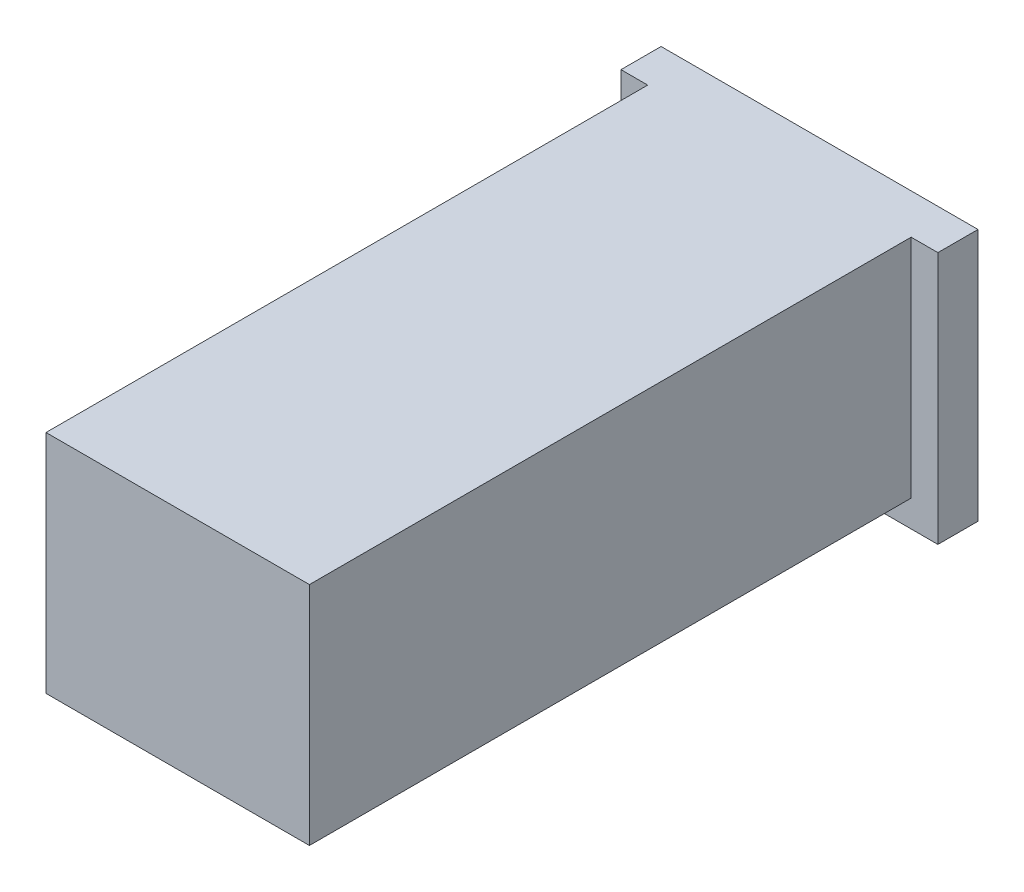
SolidWorks part; units mm, degrees
ref_plane "Alzado" through (0, 0, 0) normal (0, 0, 1) x (1, 0, 0)
ref_plane "Planta" through (0, 0, 0) normal (0, 1, 0) x (1, 0, 0)
ref_plane "Vista lateral" through (0, 0, 0) normal (1, 0, 0) x (0, 0, -1)
sketch "Croquis1" plane through (0, 0, 0) normal (0, 0, 1) x (1, 0, 0)
  line L1 (-492.5, -422.5) -> (492.5, -422.5)
  line L2 (-492.5, -422.5) -> (-492.5, 422.5)
  line L3 (-492.5, 422.5) -> (492.5, 422.5)
  line L4 (492.5, -422.5) -> (492.5, 422.5)
  line L5 (-492.5, -422.5) -> (492.5, 422.5) construction
  line L6 (-492.5, 422.5) -> (492.5, -422.5) construction
  line L7 (-422.5, -352.5) -> (422.5, -352.5)
  line L8 (-422.5, -352.5) -> (-422.5, 352.5)
  line L9 (-422.5, 352.5) -> (422.5, 352.5)
  line L10 (422.5, -352.5) -> (422.5, 352.5)
  line L11 (-422.5, -352.5) -> (422.5, 352.5) construction
  line L12 (-422.5, 352.5) -> (422.5, -352.5) construction
  point P0 (0, 0)
  point P6 (0, 0)
  dimension "D1" = 985
  dimension "D2" = 845
  dimension "D3" = 70
  dimension "D4" = 70
extrude "Saliente-Extruir1" add sketch "Croquis1" along normal blind 95
sketch "Croquis2" plane through (0, 0, 95) normal (0, 0, 1) x (1, 0, 0)
  line L0 (-492.5, -422.5) -> (-442.5, -422.5)
  line L1 (-492.5, -422.5) -> (492.5, -422.5) construction
  line L2 (-442.5, -422.5) -> (-442.5, -405.5)
  line L3 (-442.5, -405.5) -> (-416.5, -405.5)
  line L4 (-416.5, -405.5) -> (-416.5, -403.5)
  line L5 (-416.5, -403.5) -> (-444.5, -403.5)
  line L6 (-444.5, -403.5) -> (-444.5, -420.5)
  line L7 (-444.5, -420.5) -> (-490.5, -420.5)
  line L8 (-490.5, -420.5) -> (-490.5, 420.5)
  line L9 (-492.5, 422.5) -> (-492.5, -422.5) construction
  line L10 (-492.5, -422.5) -> (-492.5, 422.5)
  line L11 (492.5, 422.5) -> (-492.5, 422.5) construction
  line L12 (-490.5, 420.5) -> (490.5, 420.5)
  line L13 (492.5, 422.5) -> (-492.5, 422.5)
  line L14 (492.5, 422.5) -> (492.5, -422.5)
  line L15 (490.5, 420.5) -> (490.5, -405.5)
  line L16 (492.5, -422.5) -> (442.5, -422.5)
  line L17 (442.5, -422.5) -> (442.5, -405.5)
  line L18 (442.5, -405.5) -> (416.5, -405.5)
  line L19 (416.5, -405.5) -> (416.5, -403.5)
  line L20 (416.5, -403.5) -> (444.5, -403.5)
  line L21 (444.5, -403.5) -> (444.5, -420.5)
  line L22 (444.5, -420.5) -> (490.5, -420.5)
  line L23 (490.5, -420.5) -> (490.5, -405.5)
  dimension "D1" = 50
  dimension "D2" = 17
  dimension "D3" = 26
  dimension "D4" = 2
  dimension "D5" = 2
  dimension "D6" = 2
  dimension "D7" = 2
  dimension "D8" = 2
  dimension "D9" = 2
  dimension "D10" = 50
  dimension "D11" = 17
  dimension "D12" = 26
  dimension "D13" = 2
  dimension "D14" = 2
  dimension "D15" = 2
extrude "Saliente-Extruir2" add sketch "Croquis2" along normal blind 1905
sketch "Croquis4" plane through (0, 0, 95) normal (0, 0, 1) x (1, 0, 0)
  line L0 (-442.5, -405.5) -> (-442.5, -407.5)
  line L1 (-442.5, -422.5) -> (-442.5, -405.5) construction
  line L2 (-442.5, -407.5) -> (-414.5, -407.5)
  line L3 (-416.5, -405.5) -> (-416.5, -403.5) construction
  line L4 (-414.5, -407.5) -> (-414.5, -357.5)
  line L5 (-442.5, -405.5) -> (-416.5, -405.5)
  line L6 (-416.5, -405.5) -> (-416.5, -357.5)
  line L8 (0, -422.5) -> (0, -296.3309) construction
  line L9 (-442.5, -422.5) -> (442.5, -422.5) construction
  line L11 (416.5, -405.5) -> (416.5, -357.5)
  line L12 (442.5, -405.5) -> (416.5, -405.5)
  line L13 (414.5, -407.5) -> (414.5, -357.5)
  line L14 (442.5, -407.5) -> (414.5, -407.5)
  line L15 (442.5, -405.5) -> (442.5, -407.5)
  line L16 (-414.5, -357.5) -> (414.5, -357.5)
  line L17 (416.5, -357.5) -> (416.5, -355.5)
  line L18 (416.5, -355.5) -> (-416.5, -355.5)
  line L19 (-416.5, -355.5) -> (-416.5, -357.5)
  dimension "D1" = 2
  dimension "D2" = 2
  dimension "D3" = 50
  dimension "D4" = 2
extrude "Saliente-Extruir4" add sketch "Croquis4" along normal blind 1903
sketch "Croquis3" plane through (0, 422.5, 0) normal (0, 1, 0) x (1, 0, 0)
  line L0 (492.5, -2000) -> (-492.5, -2000)
  line L1 (-492.5, -2000) -> (-492.5, -1998)
  line L2 (-492.5, -2000) -> (-492.5, 0) construction
  line L3 (-492.5, -1998) -> (492.5, -1998)
  line L4 (492.5, -2000) -> (492.5, 0) construction
  line L5 (492.5, -1998) -> (492.5, -2000)
  dimension "D1" = 2
extrude "Saliente-Extruir3" add sketch "Croquis3" against normal up to surface (845 mm away) up to face at (0, -422.5, 1023.75)
sketch "Croquis5" plane through (0, -357.5, 0) normal (0, -1, 0) x (1, 0, 0)
  line L0 (-414.5, 1998) -> (-414.5, 95) construction
  line L1 (-166.5, 1523) -> (166.5, 1523)
  line L2 (-166.5, 1523) -> (-166.5, 1905)
  line L3 (-166.5, 1905) -> (166.5, 1905)
  line L4 (166.5, 1523) -> (166.5, 1905)
  line L5 (-166.5, 1523) -> (166.5, 1905) construction
  line L6 (-166.5, 1905) -> (166.5, 1523) construction
  line L9 (-442.5, 1998) -> (442.5, 1998) construction
  point P0 (0, 1714)
  dimension "D1" = 382
  dimension "D2" = 333
  dimension "D3" = 248
  dimension "D4" = 93
extrude "Saliente-Extruir5" add sketch "Croquis5" along normal blind 20
sketch "Croquis6" plane through (0, -377.5, 0) normal (0, -1, 0) x (1, 0, 0)
  line L0 (166.5, 1905) -> (-166.5, 1905) construction
  line L1 (-151.5, 1538) -> (151.5, 1538)
  line L2 (-151.5, 1538) -> (-151.5, 1890)
  line L3 (-151.5, 1890) -> (151.5, 1890)
  line L4 (151.5, 1538) -> (151.5, 1890)
  line L5 (-151.5, 1538) -> (151.5, 1890) construction
  line L6 (-151.5, 1890) -> (151.5, 1538) construction
  line L7 (166.5, 1523) -> (166.5, 1905) construction
  line L8 (-166.5, 1905) -> (-166.5, 1523) construction
  line L9 (-166.5, 1523) -> (166.5, 1523) construction
  point P0 (0, 1714)
  dimension "D1" = 15
  dimension "D2" = 15
  dimension "D3" = 15
  dimension "D4" = 15
extrude "Saliente-Extruir6" add sketch "Croquis6" along normal blind 20
sketch "Croquis9" plane through (0, -397.5, 0) normal (0, -1, 0) x (1, 0, 0)
  line L1 (-34.1154, 1823.4833) -> (-15.8109, 1823.4833)
  line L2 (-34.1154, 1823.4833) -> (-34.1154, 1871.8073)
  line L3 (-34.1154, 1871.8073) -> (-15.8109, 1871.8073)
  line L4 (-15.8109, 1823.4833) -> (-15.8109, 1871.8073)
  line L5 (-34.1154, 1823.4833) -> (-15.8109, 1871.8073) construction
  line L6 (-34.1154, 1871.8073) -> (-15.8109, 1823.4833) construction
  line L7 (-8.7172, 1823.4833) -> (8.7172, 1823.4833)
  line L8 (-8.7172, 1823.4833) -> (-8.7172, 1871.8073)
  line L9 (-8.7172, 1871.8073) -> (8.7172, 1871.8073)
  line L10 (8.7172, 1823.4833) -> (8.7172, 1871.8073)
  line L11 (-8.7172, 1823.4833) -> (8.7172, 1871.8073) construction
  line L12 (-8.7172, 1871.8073) -> (8.7172, 1823.4833) construction
  line L13 (18.2355, 1823.4833) -> (36.54, 1823.4833)
  line L14 (18.2355, 1823.4833) -> (18.2355, 1871.8073)
  line L15 (18.2355, 1871.8073) -> (36.54, 1871.8073)
  line L16 (36.54, 1823.4833) -> (36.54, 1871.8073)
  line L17 (18.2355, 1823.4833) -> (36.54, 1871.8073) construction
  line L18 (18.2355, 1871.8073) -> (36.54, 1823.4833) construction
  line L19 (47.5227, 1823.4833) -> (65.0951, 1823.4833)
  line L20 (47.5227, 1823.4833) -> (47.5227, 1871.8073)
  line L21 (47.5227, 1871.8073) -> (65.0951, 1871.8073)
  line L22 (65.0951, 1823.4833) -> (65.0951, 1871.8073)
  line L23 (47.5227, 1823.4833) -> (65.0951, 1871.8073) construction
  line L24 (47.5227, 1871.8073) -> (65.0951, 1823.4833) construction
  point P0 (-24.9631, 1847.6453)
  point P5 (0, 1847.6453)
  point P10 (27.3878, 1847.6453)
  point P15 (56.3089, 1847.6453)
extrude "Saliente-Extruir8" add sketch "Croquis9" along normal blind 5
sketch "Croquis10" plane through (0, -402.5, 0) normal (0, -1, 0) x (1, 0, 0)
  line L1 (-31.5489, 1864.4494) -> (-29.1067, 1864.4494)
  line L2 (-31.5489, 1864.4494) -> (-31.5489, 1867.7057)
  line L3 (-31.5489, 1867.7057) -> (-29.1067, 1867.7057)
  line L4 (-29.1067, 1864.4494) -> (-29.1067, 1867.7057)
  line L5 (-31.5489, 1864.4494) -> (-29.1067, 1867.7057) construction
  line L6 (-31.5489, 1867.7057) -> (-29.1067, 1864.4494) construction
  line L7 (-26.4609, 1864.4494) -> (-23.6116, 1864.4494)
  line L8 (-26.4609, 1864.4494) -> (-26.4609, 1867.7057)
  line L9 (-26.4609, 1867.7057) -> (-23.6116, 1867.7057)
  line L10 (-23.6116, 1864.4494) -> (-23.6116, 1867.7057)
  line L11 (-26.4609, 1864.4494) -> (-23.6116, 1867.7057) construction
  line L12 (-26.4609, 1867.7057) -> (-23.6116, 1864.4494) construction
  line L13 (-21.2711, 1864.4494) -> (-18.6253, 1864.4494)
  line L14 (-21.2711, 1864.4494) -> (-21.2711, 1867.7057)
  line L15 (-21.2711, 1867.7057) -> (-18.6253, 1867.7057)
  line L16 (-18.6253, 1864.4494) -> (-18.6253, 1867.7057)
  line L17 (-21.2711, 1864.4494) -> (-18.6253, 1867.7057) construction
  line L18 (-21.2711, 1867.7057) -> (-18.6253, 1864.4494) construction
  line L19 (-31.5489, 1857.835) -> (-29.1067, 1857.835)
  line L20 (-31.5489, 1857.835) -> (-31.5489, 1860.6843)
  line L21 (-31.5489, 1860.6843) -> (-29.1067, 1860.6843)
  line L22 (-29.1067, 1857.835) -> (-29.1067, 1860.6843)
  line L23 (-31.5489, 1857.835) -> (-29.1067, 1860.6843) construction
  line L24 (-31.5489, 1860.6843) -> (-29.1067, 1857.835) construction
  line L25 (-26.4609, 1857.835) -> (-23.6116, 1857.835)
  line L26 (-26.4609, 1857.835) -> (-26.4609, 1860.6843)
  line L27 (-26.4609, 1860.6843) -> (-23.6116, 1860.6843)
  line L28 (-23.6116, 1857.835) -> (-23.6116, 1860.6843)
  line L29 (-26.4609, 1857.835) -> (-23.6116, 1860.6843) construction
  line L30 (-26.4609, 1860.6843) -> (-23.6116, 1857.835) construction
  line L31 (-21.2711, 1857.835) -> (-18.6253, 1857.835)
  line L32 (-21.2711, 1857.835) -> (-21.2711, 1860.6843)
  line L33 (-21.2711, 1860.6843) -> (-18.6253, 1860.6843)
  line L34 (-18.6253, 1857.835) -> (-18.6253, 1860.6843)
  line L35 (-21.2711, 1857.835) -> (-18.6253, 1860.6843) construction
  line L36 (-21.2711, 1860.6843) -> (-18.6253, 1857.835) construction
  line L37 (-31.5489, 1852.7469) -> (-29.1067, 1852.7469)
  line L38 (-31.5489, 1852.7469) -> (-31.5489, 1855.1892)
  line L39 (-31.5489, 1855.1892) -> (-29.1067, 1855.1892)
  line L40 (-29.1067, 1852.7469) -> (-29.1067, 1855.1892)
  line L41 (-31.5489, 1852.7469) -> (-29.1067, 1855.1892) construction
  line L42 (-31.5489, 1855.1892) -> (-29.1067, 1852.7469) construction
  line L43 (-26.4609, 1852.7469) -> (-23.6116, 1852.7469)
  line L44 (-26.4609, 1852.7469) -> (-26.4609, 1855.1892)
  line L45 (-26.4609, 1855.1892) -> (-23.6116, 1855.1892)
  line L46 (-23.6116, 1852.7469) -> (-23.6116, 1855.1892)
  line L47 (-26.4609, 1852.7469) -> (-23.6116, 1855.1892) construction
  line L48 (-26.4609, 1855.1892) -> (-23.6116, 1852.7469) construction
  line L49 (-21.2711, 1852.7469) -> (-18.6253, 1852.7469)
  line L50 (-21.2711, 1852.7469) -> (-21.2711, 1855.1892)
  line L51 (-21.2711, 1855.1892) -> (-18.6253, 1855.1892)
  line L52 (-18.6253, 1852.7469) -> (-18.6253, 1855.1892)
  line L53 (-21.2711, 1852.7469) -> (-18.6253, 1855.1892) construction
  line L54 (-21.2711, 1855.1892) -> (-18.6253, 1852.7469) construction
  line L55 (-5.6585, 1864.4494) -> (-2.8545, 1864.4494)
  line L56 (-5.6585, 1864.4494) -> (-5.6585, 1867.7057)
  line L57 (-5.6585, 1867.7057) -> (-2.8545, 1867.7057)
  line L58 (-2.8545, 1864.4494) -> (-2.8545, 1867.7057)
  line L59 (-5.6585, 1864.4494) -> (-2.8545, 1867.7057) construction
  line L60 (-5.6585, 1867.7057) -> (-2.8545, 1864.4494) construction
  line L61 (-0.7515, 1864.4494) -> (2.2527, 1864.4494)
  line L62 (-0.7515, 1864.4494) -> (-0.7515, 1867.7057)
  line L63 (-0.7515, 1867.7057) -> (2.2527, 1867.7057)
  line L64 (2.2527, 1864.4494) -> (2.2527, 1867.7057)
  line L65 (-0.7515, 1864.4494) -> (2.2527, 1867.7057) construction
  line L66 (-0.7515, 1867.7057) -> (2.2527, 1864.4494) construction
  line L67 (4.0553, 1864.4494) -> (6.8593, 1864.4494)
  line L68 (4.0553, 1864.4494) -> (4.0553, 1867.7057)
  line L69 (4.0553, 1867.7057) -> (6.8593, 1867.7057)
  line L70 (6.8593, 1864.4494) -> (6.8593, 1867.7057)
  line L71 (4.0553, 1864.4494) -> (6.8593, 1867.7057) construction
  line L72 (4.0553, 1867.7057) -> (6.8593, 1864.4494) construction
  line L73 (-5.6585, 1857.835) -> (-2.8545, 1857.835)
  line L74 (-5.6585, 1857.835) -> (-5.6585, 1860.6843)
  line L75 (-5.6585, 1860.6843) -> (-2.8545, 1860.6843)
  line L76 (-2.8545, 1857.835) -> (-2.8545, 1860.6843)
  line L77 (-5.6585, 1857.835) -> (-2.8545, 1860.6843) construction
  line L78 (-5.6585, 1860.6843) -> (-2.8545, 1857.835) construction
  line L79 (-0.7515, 1857.835) -> (2.2527, 1857.835)
  line L80 (-0.7515, 1857.835) -> (-0.7515, 1860.6843)
  line L81 (-0.7515, 1860.6843) -> (2.2527, 1860.6843)
  line L82 (2.2527, 1857.835) -> (2.2527, 1860.6843)
  line L83 (-0.7515, 1857.835) -> (2.2527, 1860.6843) construction
  line L84 (-0.7515, 1860.6843) -> (2.2527, 1857.835) construction
  line L85 (4.3181, 1857.835) -> (6.5964, 1857.835)
  line L86 (4.3181, 1857.835) -> (4.3181, 1860.6843)
  line L87 (4.3181, 1860.6843) -> (6.5964, 1860.6843)
  line L88 (6.5964, 1857.835) -> (6.5964, 1860.6843)
  line L89 (4.3181, 1857.835) -> (6.5964, 1860.6843) construction
  line L90 (4.3181, 1860.6843) -> (6.5964, 1857.835) construction
  line L91 (19.493, 1852.7469) -> (22.3312, 1852.7469)
  line L92 (19.493, 1852.7469) -> (19.493, 1855.1892)
  line L93 (19.493, 1855.1892) -> (22.3312, 1855.1892)
  line L94 (22.3312, 1852.7469) -> (22.3312, 1855.1892)
  line L95 (19.493, 1852.7469) -> (22.3312, 1855.1892) construction
  line L96 (19.493, 1855.1892) -> (22.3312, 1852.7469) construction
  line L97 (-5.543, 1852.7469) -> (-2.97, 1852.7469)
  line L98 (-5.543, 1852.7469) -> (-5.543, 1855.1892)
  line L99 (-5.543, 1855.1892) -> (-2.97, 1855.1892)
  line L100 (-2.97, 1852.7469) -> (-2.97, 1855.1892)
  line L101 (-5.543, 1852.7469) -> (-2.97, 1855.1892) construction
  line L102 (-5.543, 1855.1892) -> (-2.97, 1852.7469) construction
  line L103 (-0.7515, 1852.7469) -> (2.2527, 1852.7469)
  line L104 (-0.7515, 1852.7469) -> (-0.7515, 1855.1892)
  line L105 (-0.7515, 1855.1892) -> (2.2527, 1855.1892)
  line L106 (2.2527, 1852.7469) -> (2.2527, 1855.1892)
  line L107 (-0.7515, 1852.7469) -> (2.2527, 1855.1892) construction
  line L108 (-0.7515, 1855.1892) -> (2.2527, 1852.7469) construction
  line L109 (4.3181, 1852.7469) -> (6.5964, 1852.7469)
  line L110 (4.3181, 1852.7469) -> (4.3181, 1855.1892)
  line L111 (4.3181, 1855.1892) -> (6.5964, 1855.1892)
  line L112 (6.5964, 1852.7469) -> (6.5964, 1855.1892)
  line L113 (4.3181, 1852.7469) -> (6.5964, 1855.1892) construction
  line L114 (4.3181, 1855.1892) -> (6.5964, 1852.7469) construction
  line L115 (19.493, 1857.835) -> (22.3312, 1857.835)
  line L116 (19.493, 1857.835) -> (19.493, 1860.6843)
  line L117 (19.493, 1860.6843) -> (22.3312, 1860.6843)
  line L118 (22.3312, 1857.835) -> (22.3312, 1860.6843)
  line L119 (19.493, 1857.835) -> (22.3312, 1860.6843) construction
  line L120 (19.493, 1860.6843) -> (22.3312, 1857.835) construction
  line L121 (19.493, 1864.4494) -> (22.3312, 1864.4494)
  line L122 (19.493, 1864.4494) -> (19.493, 1867.7057)
  line L123 (19.493, 1867.7057) -> (22.3312, 1867.7057)
  line L124 (22.3312, 1864.4494) -> (22.3312, 1867.7057)
  line L125 (19.493, 1864.4494) -> (22.3312, 1867.7057) construction
  line L126 (19.493, 1867.7057) -> (22.3312, 1864.4494) construction
  line L127 (26.32, 1864.6465) -> (29.1933, 1864.6465)
  line L128 (26.32, 1864.6465) -> (26.32, 1867.5086)
  line L129 (26.32, 1867.5086) -> (29.1933, 1867.5086)
  line L130 (29.1933, 1864.6465) -> (29.1933, 1867.5086)
  line L131 (26.32, 1864.6465) -> (29.1933, 1867.5086) construction
  line L132 (26.32, 1867.5086) -> (29.1933, 1864.6465) construction
  line L133 (31.5908, 1864.6465) -> (35.0334, 1864.6465)
  line L134 (31.5908, 1864.6465) -> (31.5908, 1867.5086)
  line L135 (31.5908, 1867.5086) -> (35.0334, 1867.5086)
  line L136 (35.0334, 1864.6465) -> (35.0334, 1867.5086)
  line L137 (31.5908, 1864.6465) -> (35.0334, 1867.5086) construction
  line L138 (31.5908, 1867.5086) -> (35.0334, 1864.6465) construction
  line L139 (26.32, 1857.835) -> (29.1933, 1857.835)
  line L140 (26.32, 1857.835) -> (26.32, 1860.6843)
  line L141 (26.32, 1860.6843) -> (29.1933, 1860.6843)
  line L142 (29.1933, 1857.835) -> (29.1933, 1860.6843)
  line L143 (26.32, 1857.835) -> (29.1933, 1860.6843) construction
  line L144 (26.32, 1860.6843) -> (29.1933, 1857.835) construction
  line L145 (32.1626, 1857.835) -> (34.4616, 1857.835)
  line L146 (32.1626, 1857.835) -> (32.1626, 1860.6843)
  line L147 (32.1626, 1860.6843) -> (34.4616, 1860.6843)
  line L148 (34.4616, 1857.835) -> (34.4616, 1860.6843)
  line L149 (32.1626, 1857.835) -> (34.4616, 1860.6843) construction
  line L150 (32.1626, 1860.6843) -> (34.4616, 1857.835) construction
  line L151 (26.32, 1852.7469) -> (29.1933, 1852.7469)
  line L152 (26.32, 1852.7469) -> (26.32, 1855.1892)
  line L153 (26.32, 1855.1892) -> (29.1933, 1855.1892)
  line L154 (29.1933, 1852.7469) -> (29.1933, 1855.1892)
  line L155 (26.32, 1852.7469) -> (29.1933, 1855.1892) construction
  line L156 (26.32, 1855.1892) -> (29.1933, 1852.7469) construction
  line L157 (32.1626, 1852.7469) -> (34.4616, 1852.7469)
  line L158 (32.1626, 1852.7469) -> (32.1626, 1855.1892)
  line L159 (32.1626, 1855.1892) -> (34.4616, 1855.1892)
  line L160 (34.4616, 1852.7469) -> (34.4616, 1855.1892)
  line L161 (32.1626, 1852.7469) -> (34.4616, 1855.1892) construction
  line L162 (32.1626, 1855.1892) -> (34.4616, 1852.7469) construction
  point P0 (-30.3278, 1866.0776)
  point P5 (-25.0362, 1866.0776)
  point P10 (-19.9482, 1866.0776)
  point P15 (-30.3278, 1859.2596)
  point P20 (-25.0362, 1859.2596)
  point P25 (-19.9482, 1859.2596)
  point P30 (-30.3278, 1853.9681)
  point P35 (-25.0362, 1853.9681)
  point P40 (-19.9482, 1853.9681)
  point P45 (-4.2565, 1866.0776)
  point P50 (0.7506, 1866.0776)
  point P55 (5.4573, 1866.0776)
  point P60 (-4.2565, 1859.2596)
  point P65 (0.7506, 1859.2596)
  point P70 (5.4573, 1859.2596)
  point P75 (20.9121, 1853.9681)
  point P80 (-4.2565, 1853.9681)
  point P85 (0.7506, 1853.9681)
  point P90 (5.4573, 1853.9681)
  point P95 (20.9121, 1859.2596)
  point P100 (20.9121, 1866.0776)
  point P105 (27.7566, 1866.0776)
  point P110 (33.3121, 1866.0776)
  point P115 (27.7566, 1859.2596)
  point P120 (33.3121, 1859.2596)
  point P125 (27.7566, 1853.9681)
  point P130 (33.3121, 1853.9681)
extrude "Saliente-Extruir9" add sketch "Croquis10" along normal blind 3
sketch "Croquis8" plane through (0, -397.5, 0) normal (0, -1, 0) x (1, 0, 0)
  line L0 (-151.5, 1890) -> (-151.5, 1820)
  line L1 (-151.5, 1890) -> (-151.5, 1538) construction
  line L2 (-151.5, 1820) -> (151.5, 1820)
  line L3 (151.5, 1538) -> (151.5, 1890) construction
  line L4 (151.5, 1820) -> (151.5, 1890)
  line L5 (151.5, 1890) -> (-151.5, 1890)
  dimension "D1" = 70
extrude "Cortar-Extruir1" cut sketch "Croquis8" against normal blind 1
sketch "Croquis11" plane through (0, -397.5, 0) normal (0, -1, 0) x (1, 0, 0)
  line L1 (-68.0953, 1553.9879) -> (-41.9843, 1553.9879)
  line L2 (-68.0953, 1553.9879) -> (-68.0953, 1775.9317)
  line L3 (-68.0953, 1775.9317) -> (-41.9843, 1775.9317)
  line L4 (-41.9843, 1553.9879) -> (-41.9843, 1775.9317)
  line L5 (-68.0953, 1553.9879) -> (-41.9843, 1775.9317) construction
  line L6 (-68.0953, 1775.9317) -> (-41.9843, 1553.9879) construction
  point P0 (-55.0398, 1664.9598)
extrude "Cortar-Extruir2" cut sketch "Croquis11" against normal blind 3
sketch "Croquis12" plane through (0, -397.5, 0) normal (0, -1, 0) x (1, 0, 0)
  line L1 (9.9223, 1761.0623) -> (52.8459, 1761.0623)
  line L2 (9.9223, 1761.0623) -> (9.9223, 1781.591)
  line L3 (9.9223, 1781.591) -> (52.8459, 1781.591)
  line L4 (52.8459, 1761.0623) -> (52.8459, 1781.591)
  line L5 (9.9223, 1761.0623) -> (52.8459, 1781.591) construction
  line L6 (9.9223, 1781.591) -> (52.8459, 1761.0623) construction
  line L7 (9.9223, 1678.0144) -> (52.8459, 1678.0144)
  line L8 (9.9223, 1678.0144) -> (9.9223, 1732.1355)
  line L9 (9.9223, 1732.1355) -> (52.8459, 1732.1355)
  line L10 (52.8459, 1678.0144) -> (52.8459, 1732.1355)
  line L11 (9.9223, 1678.0144) -> (52.8459, 1732.1355) construction
  line L12 (9.9223, 1732.1355) -> (52.8459, 1678.0144) construction
  line L13 (9.9223, 1598.6991) -> (52.8459, 1598.6991)
  line L14 (9.9223, 1598.6991) -> (9.9223, 1652.8202)
  line L15 (9.9223, 1652.8202) -> (52.8459, 1652.8202)
  line L16 (52.8459, 1598.6991) -> (52.8459, 1652.8202)
  line L17 (9.9223, 1598.6991) -> (52.8459, 1652.8202) construction
  line L18 (9.9223, 1652.8202) -> (52.8459, 1598.6991) construction
  line L19 (77.107, 1761.0623) -> (106.9669, 1761.0623)
  line L20 (77.107, 1761.0623) -> (77.107, 1781.591)
  line L21 (77.107, 1781.591) -> (106.9669, 1781.591)
  line L22 (106.9669, 1761.0623) -> (106.9669, 1781.591)
  line L23 (77.107, 1761.0623) -> (106.9669, 1781.591) construction
  line L24 (77.107, 1781.591) -> (106.9669, 1761.0623) construction
  line L25 (77.107, 1689.2119) -> (106.9669, 1689.2119)
  line L26 (77.107, 1689.2119) -> (77.107, 1720.9381)
  line L27 (77.107, 1720.9381) -> (106.9669, 1720.9381)
  line L28 (106.9669, 1689.2119) -> (106.9669, 1720.9381)
  line L29 (77.107, 1689.2119) -> (106.9669, 1720.9381) construction
  line L30 (77.107, 1720.9381) -> (106.9669, 1689.2119) construction
  line L31 (67.8123, 1628.6523) -> (116.2616, 1628.6523)
  line L32 (67.8123, 1628.6523) -> (67.8123, 1648.9944)
  line L33 (67.8123, 1648.9944) -> (116.2616, 1648.9944)
  line L34 (116.2616, 1628.6523) -> (116.2616, 1648.9944)
  line L35 (67.8123, 1628.6523) -> (116.2616, 1648.9944) construction
  line L36 (67.8123, 1648.9944) -> (116.2616, 1628.6523) construction
  line L37 (9.9223, 1562.3073) -> (52.8459, 1562.3073)
  line L38 (9.9223, 1562.3073) -> (9.9223, 1582.836)
  line L39 (9.9223, 1582.836) -> (52.8459, 1582.836)
  line L40 (52.8459, 1562.3073) -> (52.8459, 1582.836)
  line L41 (9.9223, 1562.3073) -> (52.8459, 1582.836) construction
  line L42 (9.9223, 1582.836) -> (52.8459, 1562.3073) construction
  point P0 (31.3841, 1771.3266)
  point P5 (31.3841, 1705.075)
  point P10 (31.3841, 1625.7596)
  point P15 (92.037, 1771.3266)
  point P20 (92.037, 1705.075)
  point P25 (92.037, 1638.8233)
  point P30 (31.3841, 1572.5717)
extrude "Saliente-Extruir10" add sketch "Croquis12" along normal blind 1
sketch "Croquis13" plane through (0, -398.5, 0) normal (0, -1, 0) x (1, 0, 0)
  circle A0 centre (19.3177, 1772.6688) radius 6.5979
  circle A1 centre (19.3177, 1772.6688) radius 3.4774
extrude "Saliente-Extruir11" add sketch "Croquis13" along normal blind 1
sketch "Croquis16" plane through (0, -398.5, 0) normal (0, -1, 0) x (1, 0, 0)
  line L1 (26.7756, 1600.2785) -> (34.9888, 1600.2785)
  line L2 (26.7756, 1600.2785) -> (26.7756, 1627.4357)
  line L3 (26.7756, 1627.4357) -> (34.9888, 1627.4357)
  line L4 (34.9888, 1600.2785) -> (34.9888, 1627.4357)
  line L5 (26.7756, 1600.2785) -> (34.9888, 1627.4357) construction
  line L6 (26.7756, 1627.4357) -> (34.9888, 1600.2785) construction
  circle A0 centre (30.8822, 1692.2694) radius 13.3867
  circle A1 centre (30.8822, 1692.2694) radius 8.6503
  point P3 (30.8822, 1613.8571)
extrude "Saliente-Extruir12" add sketch "Croquis16" along normal blind 1
sketch "Croquis17" plane through (0, -398.5, 0) normal (0, -1, 0) x (1, 0, 0)
  line L0 (26.4141, 1766.789) -> (51.3593, 1766.789) construction
  text T0 "OPEN" font "Century Gothic" height in points 24
extrude "Saliente-Extruir13" add sketch "Croquis17" along normal blind 1
sketch "Croquis18" plane through (0, -398.5, 0) normal (0, -1, 0) x (1, 0, 0)
  line L0 (9.9223, 1709.4809) -> (52.8459, 1709.4809) construction
  line L1 (9.9223, 1732.1355) -> (9.9223, 1678.0144) construction
  line L2 (52.8459, 1678.0144) -> (52.8459, 1732.1355) construction
  text T0 "PUSH OFF" font "Century Gothic" height in points 24
extrude "Saliente-Extruir14" add sketch "Croquis18" along normal blind 1
sketch "Croquis19" plane through (0, -398.5, 0) normal (0, -1, 0) x (1, 0, 0)
  line L0 (9.9223, 1631.4933) -> (52.8459, 1631.4933) construction
  line L1 (9.9223, 1652.8202) -> (9.9223, 1598.6991) construction
  line L2 (52.8459, 1598.6991) -> (52.8459, 1652.8202) construction
  text T0 "PUSH ON" font "Century Gothic" height in points 24
extrude "Saliente-Extruir15" add sketch "Croquis19" along normal blind 1
sketch "Croquis20" plane through (0, -394.5, 0) normal (0, -1, 0) x (1, 0, 0)
  line L1 (-64.747, 1555.8626) -> (-45.3326, 1555.8626)
  line L2 (-64.747, 1555.8626) -> (-64.747, 1601.4886)
  line L3 (-64.747, 1601.4886) -> (-45.3326, 1601.4886)
  line L4 (-45.3326, 1555.8626) -> (-45.3326, 1601.4886)
  line L5 (-64.747, 1555.8626) -> (-45.3326, 1601.4886) construction
  line L6 (-64.747, 1601.4886) -> (-45.3326, 1555.8626) construction
  line L7 (-64.747, 1737.4334) -> (-45.3326, 1737.4334)
  line L8 (-64.747, 1737.4334) -> (-64.747, 1767.0393)
  line L9 (-64.747, 1767.0393) -> (-45.3326, 1767.0393)
  line L10 (-45.3326, 1737.4334) -> (-45.3326, 1767.0393)
  line L11 (-64.747, 1737.4334) -> (-45.3326, 1767.0393) construction
  line L12 (-64.747, 1767.0393) -> (-45.3326, 1737.4334) construction
  point P0 (-55.0398, 1578.6756)
  point P5 (-55.0398, 1752.2364)
extrude "Cortar-Extruir3" cut sketch "Croquis20" against normal blind 5
sketch "Croquis21" plane through (0, -357.5, 0) normal (0, -1, 0) x (1, 0, 0)
  line L0 (-166.5, 1523) -> (166.5, 1523) construction
  line L1 (-414.5, 1998) -> (-414.5, 95) construction
  circle A0 centre (-4.5, 994) radius 15
  dimension "D2" = 30
  dimension "D1" = 529
  dimension "D3" = 410
extrude "Saliente-Extruir16" add sketch "Croquis21" along normal blind 10
sketch "Croquis22" plane through (0, -357.5, 0) normal (0, -1, 0) x (1, 0, 0)
  circle A0 centre (146.5, 994) radius 15
  circle A1 centre (-155.5, 994) radius 32.5
  circle A2 centre (-4.5, 994) radius 15 construction
  circle A3 centre (-4.5, 994) radius 15 construction
  circle A4 centre (-155.5, 994) radius 25.5056
  dimension "D1" = 30
  dimension "D2" = 151
  dimension "D3" = 151
  dimension "D4" = 65
extrude "Saliente-Extruir17" add sketch "Croquis22" along normal blind 10
sketch "Croquis23" plane through (0, -357.5, 0) normal (0, -1, 0) x (1, 0, 0)
  line L1 (-188.5549, 960.1893) -> (-122.4451, 960.1893)
  line L2 (-188.5549, 960.1893) -> (-188.5549, 1027.8107)
  line L3 (-188.5549, 1027.8107) -> (-122.4451, 1027.8107)
  line L4 (-122.4451, 960.1893) -> (-122.4451, 1027.8107)
  line L5 (-188.5549, 960.1893) -> (-122.4451, 1027.8107) construction
  line L6 (-188.5549, 1027.8107) -> (-122.4451, 960.1893) construction
  point P0 (-155.5, 994)
extrude "Saliente-Extruir18" add sketch "Croquis23" along normal blind 4
sketch "Croquis24" plane through (0, -361.5, 0) normal (0, -1, 0) x (1, 0, 0)
  line L0 (-150.0392, 998.484) -> (-157.2551, 993.363)
  line L1 (-157.2551, 993.363) -> (-150.0392, 989.4058)
  line L2 (-150.0392, 989.4058) -> (-130.4116, 989.4058)
  line L3 (-150.0392, 998.484) -> (-130.3916, 998.484)
  line L4 (-130.3916, 998.484) -> (-123.3108, 998.484)
  line L5 (-123.3108, 998.484) -> (-123.3108, 989.516)
  line L6 (-123.3108, 989.516) -> (-130.4116, 989.4058)
  circle A0 centre (-155.5, 994) radius 25.5056 construction
  circle A1 centre (-155.5, 994) radius 32.5 construction
extrude "Saliente-Extruir19" add sketch "Croquis24" along normal blind 8
sketch "Croquis25" plane through (0, -357.5, 0) normal (0, -1, 0) x (1, 0, 0)
  line L0 (0, 95) -> (0, 1383.1517) construction
  line L1 (-442.5, 95) -> (442.5, 95) construction
  line L2 (0, 1373) -> (-80, 1373)
  line L3 (0, 1373) -> (80, 1373)
  line L4 (-166.5, 1523) -> (166.5, 1523) construction
  line L5 (-80, 1373) -> (-80, 1255.5)
  line L6 (-80, 1255.5) -> (80, 1255.5)
  line L7 (80, 1255.5) -> (80, 1373)
  point P10 (-40, 1373)
  dimension "D1" = 80
  dimension "D2" = 80
  dimension "D3" = 150
  dimension "D4" = 117.5
extrude "Cortar-Extruir4" cut sketch "Croquis25" against normal blind 2
sketch "Croquis26" plane through (0, 0, 0) normal (0, 0, -1) x (-1, 0, 0)
  line L0 (492.5, -422.5) -> (-492.5, -422.5) construction
  line L1 (492.5, 422.5) -> (-492.5, 422.5)
  line L2 (492.5, 422.5) -> (492.5, -422.5)
  line L3 (492.5, -422.5) -> (-492.5, -422.5)
  line L4 (-492.5, 422.5) -> (-492.5, -422.5)
  line L5 (492.5, 422.5) -> (-492.5, -422.5) construction
  line L6 (492.5, -422.5) -> (-492.5, 422.5) construction
  point P0 (0, 0)
extrude "Saliente-Extruir20" add sketch "Croquis26" along normal blind 250
sketch "Croquis27" plane through (0, 0, -250) normal (0, 0, -1) x (-1, 0, 0)
  line L0 (492.5, 422.5) -> (592.5, 422.5)
  line L1 (592.5, -522.5) -> (-592.5, -522.5)
  line L2 (592.5, -522.5) -> (592.5, 422.5)
  line L3 (492.5, 422.5) -> (-492.5, 422.5)
  line L4 (-592.5, -522.5) -> (-592.5, 422.5)
  line L5 (592.5, -522.5) -> (0, 0) construction
  line L6 (0, 0) -> (-592.5, -522.5) construction
  line L7 (-492.5, 422.5) -> (-592.5, 422.5)
  line L8 (492.5, -422.5) -> (492.5, 422.5) construction
  line L10 (-492.5, -422.5) -> (492.5, -422.5) construction
  point P0 (0, 0)
  dimension "D1" = 100
  dimension "D2" = 100
extrude "Saliente-Extruir21" add sketch "Croquis27" along normal blind 150
sketch "Croquis28" plane through (0, 0, 95) normal (0, 0, 1) x (1, 0, 0)
  line L0 (-414.5, -357.5) -> (-414.5, -407.5)
  line L1 (-414.5, -407.5) -> (-442.5, -407.5)
  line L2 (-442.5, -407.5) -> (-442.5, -422.5)
  line L3 (-442.5, -422.5) -> (442.5, -422.5)
  line L4 (442.5, -422.5) -> (442.5, -407.5)
  line L5 (442.5, -407.5) -> (414.5, -407.5)
  line L6 (414.5, -407.5) -> (414.5, -357.5)
  line L7 (414.5, -357.5) -> (-414.5, -357.5)
extrude "Cortar-Extruir5" cut sketch "Croquis28" against normal up to surface (345 mm away) up to face at (0, -25, -250)
